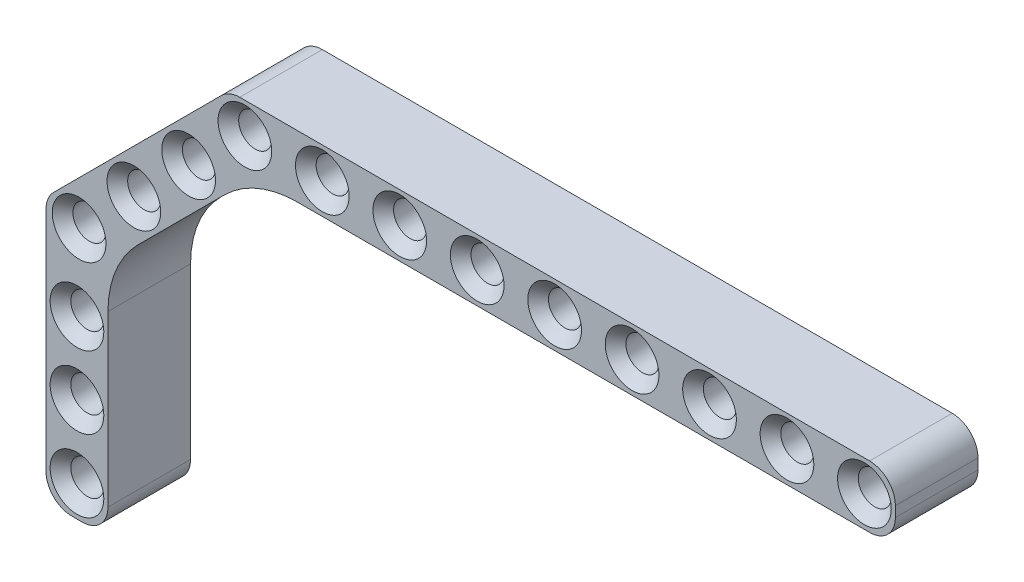
SolidWorks part; units mm, degrees
ref_plane "Front Plane" through (0, 0, 0) normal (0, 0, 1) x (1, 0, 0)
ref_plane "Top Plane" through (0, 0, 0) normal (0, 1, 0) x (1, 0, 0)
ref_plane "Right Plane" through (0, 0, 0) normal (1, 0, 0) x (0, 0, -1)
sketch "Sketch1" plane through (0, 0, 0) normal (0, 0, 1) x (1, 0, 0)
  line L1 (-0.5, 3) -> (60.5, 3)
  line L2 (-3, 0.5) -> (-3, -0.5)
  line L3 (-0.5, -3) -> (60.5, -3)
  line L4 (63, 0.5) -> (63, -0.5)
  circle A0 centre (0, 0) radius 1.6
  arc A1 (60.5, -3) -> (63, -0.5) centre (60.5, -0.5) ccw
  arc A2 (60.5, 3) -> (63, 0.5) centre (60.5, 0.5) cw
  arc A3 (-3, -0.5) -> (-0.5, -3) centre (-0.5, -0.5) ccw
  arc A4 (-0.5, 3) -> (-3, 0.5) centre (-0.5, 0.5) ccw
  circle A5 centre (7.5, 0) radius 1.6
  circle A6 centre (15, 0) radius 1.6
  circle A7 centre (22.5, 0) radius 1.6
  circle A8 centre (30, 0) radius 1.6
  circle A9 centre (37.5, 0) radius 1.6
  circle A10 centre (45, 0) radius 1.6
  circle A11 centre (52.5, 0) radius 1.6
  circle A12 centre (60, 0) radius 1.6
  point P8 (-3, 0)
  point P14 (-3, -3)
  point P17 (-3, 3)
  dimension "D1" = 3.2
  dimension "D4" = 2.5
  dimension "D2" = 6
  dimension "D3" = 3
  dimension "D6" = 7.5
  dimension "D5" = 9
extrude "Boss-Extrude1" add sketch "Sketch1" along normal blind 8
chamfer "Chamfer1" distance 1 angle 45 10 edges at (31.6, 0, 0) (31.6, 0, 8) (24.1, 0, 0) (24.1, 0, 8) (16.6, 0, 0) (16.6, 0, 8) (9.1, 0, 0) (9.1, 0, 8) (1.6, 0, 0) (1.6, 0, 8)
sketch "Sketch2" plane through (0, 0, 8) normal (0, 0, 1) x (1, 0, 0)
  line L0 (-2.2678, 2.2678) -> (-18.5292, -13.9937)
  line L1 (-18.5292, -17.5292) -> (-17.8221, -18.2363)
  line L2 (-14.2866, -18.2363) -> (0.9497, -3)
  line L4 (-0.5, -3) -> (60.5, -3) construction
  arc A0 (-0.5, 3) -> (-3, 0.5) centre (-0.5, 0.5) ccw construction
  circle A1 centre (-5.4477, -5.1548) radius 1.6
  circle A2 centre (-10.751, -10.4581) radius 1.6
  circle A3 centre (-16.0543, -15.7614) radius 1.6
  arc A4 (-18.5292, -13.9937) -> (-18.5292, -17.5292) centre (-16.7614, -15.7614) ccw
  arc A5 (-17.8221, -18.2363) -> (-14.2866, -18.2363) centre (-16.0543, -16.4685) ccw
  point P18 (-20.297, -15.7614)
  point P21 (-16.0543, -20.0041)
  arc M15 (-0.5, 3) -> (-3, 0.5) centre (-0.5, 0.5) ccw
  line M16 (-3, 0.5) -> (-3, -0.5)
  arc M17 (-3, -0.5) -> (-0.5, -3) centre (-0.5, -0.5) ccw
  line M18 (-0.5, -3) -> (60.5, -3)
  dimension "D3" = 3.2
  dimension "D8" = 2.5
  dimension "D1" = 6
  dimension "D2" = 45
  dimension "D4" = 3
  dimension "D5" = 7.5
  dimension "D7" = 3
  dimension "D6" = 3
extrude "Boss-Extrude3" add sketch "Sketch2" against normal blind 8 contours L1 A5 L2 L0 A4 A1 A2 A3 M18 M17 M16 M15
fillet "Fillet1" radius 10 1 edges at (0.9497, -3, 4)
chamfer "Chamfer2" distance 1 angle 45 6 edges at (-14.4543, -15.7614, 8) (-14.4543, -15.7614, 0) (-9.151, -10.4581, 8) (-9.151, -10.4581, 0) (-3.8477, -5.1548, 8) (-3.8477, -5.1548, 0)
chamfer "Chamfer3" distance 1 angle 45 4 edges at (46.6, 0, 0) (46.6, 0, 8) (39.1, 0, 0) (39.1, 0, 8)
chamfer "Chamfer4" distance 1 angle 45 4 edges at (61.6, 0, 0) (61.6, 0, 8) (54.1, 0, 0) (54.1, 0, 8)
sketch "Sketch3" plane through (0, 0, 8) normal (0, 0, 1) x (1, 0, 0)
  line L0 (-14.2866, -18.2363) -> (-1.9792, -5.9289) construction
  line L2 (-19.2614, -15.7614) -> (-19.2614, -37.7614)
  line L3 (-16.7614, -40.2614) -> (-15.7614, -40.2614)
  line L4 (-13.2614, -17.2112) -> (-13.2614, -37.7614)
  arc A0 (-18.5292, -13.9937) -> (-18.5292, -17.5292) centre (-16.7614, -15.7614) ccw construction
  circle A1 centre (-16.2614, -23.2614) radius 1.6
  circle A2 centre (-16.0543, -15.7614) radius 1.6 construction
  circle A3 centre (-16.2614, -30.2614) radius 1.6
  circle A4 centre (-16.2614, -37.2614) radius 1.6
  arc A5 (-19.2614, -37.7614) -> (-16.7614, -40.2614) centre (-16.7614, -37.7614) ccw
  arc A6 (-15.7614, -40.2614) -> (-13.2614, -37.7614) centre (-15.7614, -37.7614) ccw
  point P14 (-16.2614, -40.2614)
  point P20 (-19.2614, -40.2614)
  point P23 (-13.2614, -40.2614)
  arc M22 (-18.5292, -13.9937) -> (-18.5292, -17.5292) centre (-16.7614, -15.7614) ccw
  line M23 (-18.5292, -17.5292) -> (-17.8221, -18.2363)
  arc M24 (-17.8221, -18.2363) -> (-14.2866, -18.2363) centre (-16.0543, -16.4685) ccw
  line M25 (-14.2866, -18.2363) -> (-1.9792, -5.9289)
  dimension "D3" = 3.2
  dimension "D6" = 2.5
  dimension "D1" = 6
  dimension "D2" = 7.5
  dimension "D5" = 3
  dimension "D4" = 3
extrude "Boss-Extrude4" add sketch "Sketch3" against normal blind 8 contours L3 A6 L4 L2 A5 A1 A3 A4 M25 M24 M23 M22
chamfer "Chamfer5" distance 1 angle 45 6 edges at (-14.6614, -23.2614, 8) (-14.6614, -23.2614, 0) (-14.6614, -30.2614, 8) (-14.6614, -30.2614, 0) (-14.6614, -37.2614, 8) (-14.6614, -37.2614, 0)
fillet "Fillet2" radius 10 1 edges at (-13.2614, -17.2112, 4)
